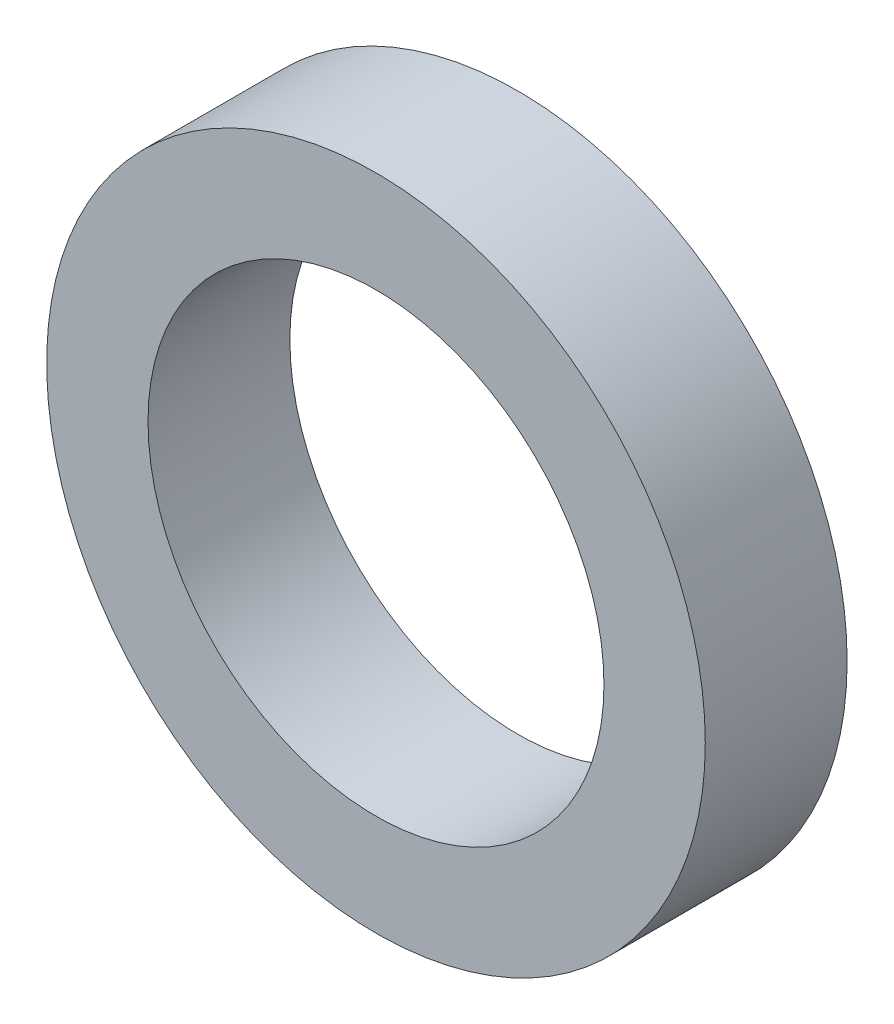
SolidWorks part; units mm, degrees
ref_plane "前视基准面" through (0, 0, 0) normal (0, 0, 1) x (1, 0, 0)
ref_plane "上视基准面" through (0, 0, 0) normal (0, 1, 0) x (1, 0, 0)
ref_plane "右视基准面" through (0, 0, 0) normal (1, 0, 0) x (0, 0, -1)
sketch "草图1" plane through (0, 0, 0) normal (0, 0, 1) x (1, 0, 0)
  circle A0 centre (0.9981, 0.4991) radius 22.5
  circle A1 centre (0.9981, 0.4991) radius 32.5
extrude "凸台-拉伸1" add sketch "草图1" along normal blind 14
